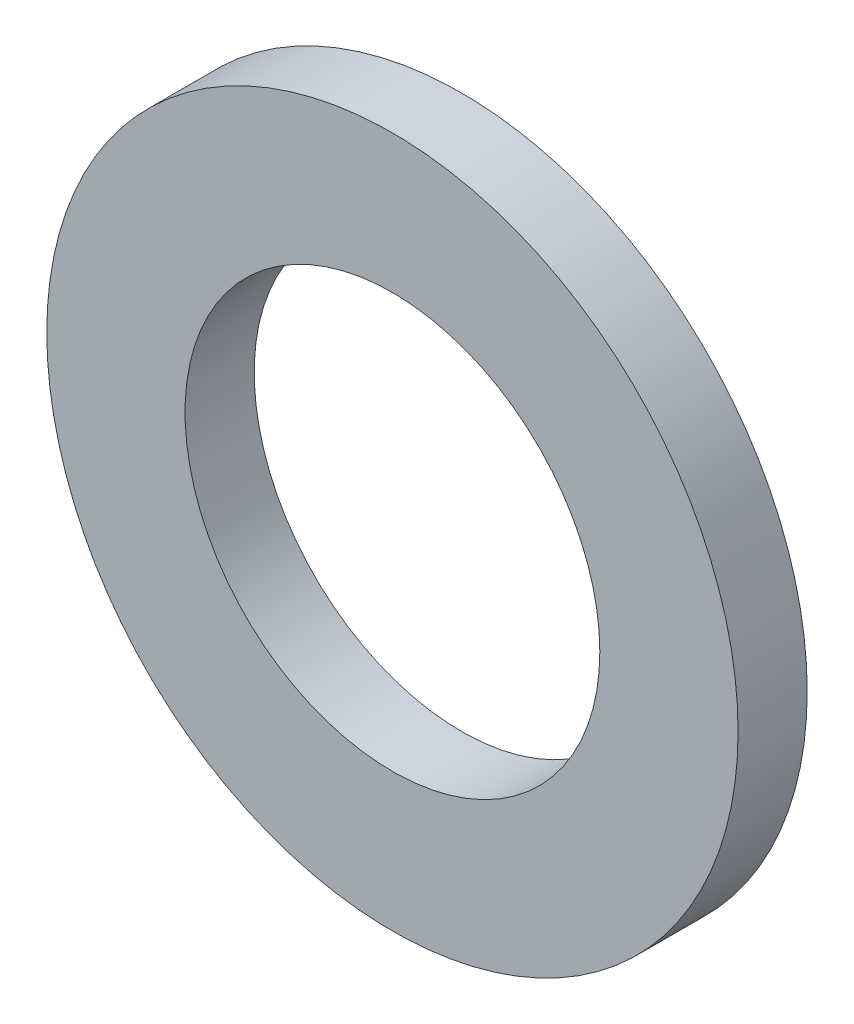
SolidWorks part; units mm, degrees
ref_plane "Plan de face" through (0, 0, 0) normal (0, 0, 1) x (1, 0, 0)
ref_plane "Plan de dessus" through (0, 0, 0) normal (0, 1, 0) x (1, 0, 0)
ref_plane "Plan de droite" through (0, 0, 0) normal (1, 0, 0) x (0, 0, -1)
sketch "Esquisse1" plane through (0, 0, 0) normal (0, 0, 1) x (1, 0, 0)
  circle A0 centre (0, 0) radius 3
  circle A1 centre (0, 0) radius 5
  dimension "D1" = 6
  dimension "D2" = 10
extrude "Boss.-Extru.1" add sketch "Esquisse1" along normal blind 1
